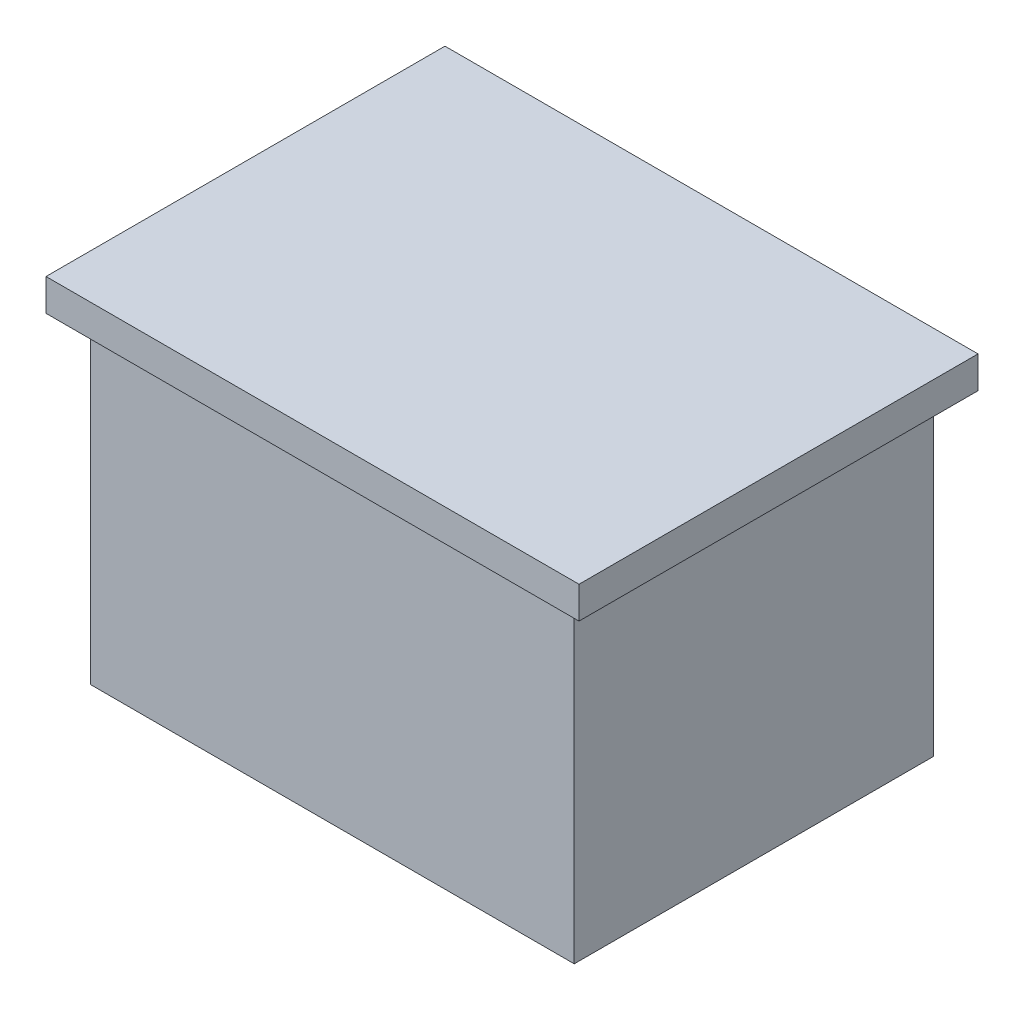
SolidWorks part; units mm, degrees
ref_plane "Front Plane" through (0, 0, 0) normal (0, 0, 1) x (1, 0, 0)
ref_plane "Top Plane" through (0, 0, 0) normal (0, 1, 0) x (1, 0, 0)
ref_plane "Right Plane" through (0, 0, 0) normal (1, 0, 0) x (0, 0, -1)
sketch "Sketch1" plane through (0, 0, 0) normal (0, 1, 0) x (1, 0, 0)
  line L1 (-15.15, -11.25) -> (15.15, -11.25)
  line L2 (-15.15, -11.25) -> (-15.15, 11.25)
  line L3 (-15.15, 11.25) -> (15.15, 11.25)
  line L4 (15.15, -11.25) -> (15.15, 11.25)
  line L5 (-15.15, -11.25) -> (15.15, 11.25) construction
  line L6 (-15.15, 11.25) -> (15.15, -11.25) construction
  point P0 (0, 0)
  dimension "D1" = 30.3
  dimension "D2" = 22.5
extrude "Boss-Extrude1" add sketch "Sketch1" along normal blind 20
sketch "Sketch2" plane through (0, 20, 0) normal (0, 1, 0) x (1, 0, 0)
  line L1 (-16.7, -12.5) -> (16.7, -12.5)
  line L2 (-16.7, -12.5) -> (-16.7, 12.5)
  line L3 (-16.7, 12.5) -> (16.7, 12.5)
  line L4 (16.7, -12.5) -> (16.7, 12.5)
  line L5 (-16.7, -12.5) -> (16.7, 12.5) construction
  line L6 (-16.7, 12.5) -> (16.7, -12.5) construction
  point P0 (0, 0)
  dimension "D1" = 33.4
  dimension "D2" = 25
extrude "Boss-Extrude2" add sketch "Sketch2" along normal blind 2
